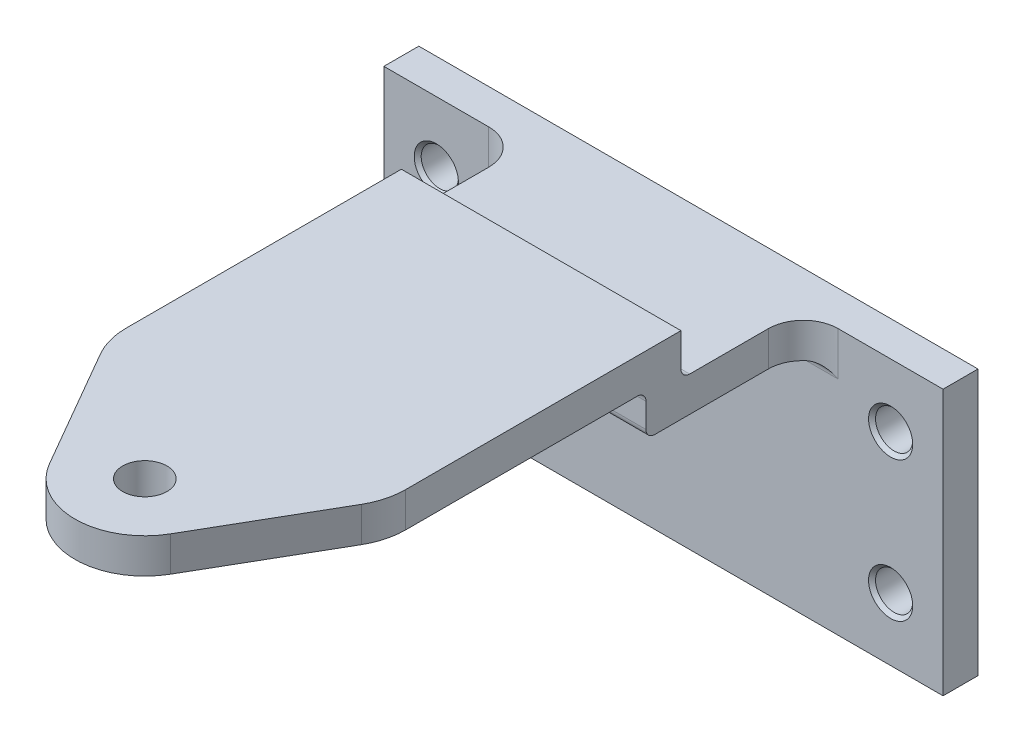
SolidWorks part; units mm, degrees
material "6061-T6 (SS)"
ref_plane "Front Plane" through (0, 0, 0) normal (0, 0, 1) x (1, 0, 0)
ref_plane "Top Plane" through (0, 0, 0) normal (0, 1, 0) x (1, 0, 0)
ref_plane "Right Plane" through (0, 0, 0) normal (1, 0, 0) x (0, 0, -1)
sketch "Sketch1" plane through (0, 0, 0) normal (0, 1, 0) x (1, 0, 0)
  line L0 (0, 0) -> (0, 67.2737) construction
  line L1 (-25.4, 50.8) -> (25.4, 50.8)
  line L2 (25.4, 50.8) -> (25.4, 18.5941)
  line L3 (25.4, 18.5941) -> (10.9985, -6.35)
  line L4 (0, 0) -> (41.2147, 0) construction
  line L5 (-25.4, 18.5941) -> (-10.9985, -6.35)
  line L6 (-25.4, 50.8) -> (-25.4, 18.5941)
  circle A0 centre (0, 0) radius 4.0323
  arc A1 (-10.9985, -6.35) -> (10.9985, -6.35) centre (0, 0) ccw
  point P13 (0, 50.8)
  dimension "D1" = 8.0645
  dimension "D2" = 25.4
  dimension "D3" = 50.8
  dimension "D4" = 50.8
  dimension "D5" = 60
extrude "Boss-Extrude1" add sketch "Sketch1" along normal mid plane 6.35
fillet "Fillet1" radius 12.7 2 edges at (25.4, 0, -18.5941) (-25.4, 0, -18.5941)
sketch "Sketch2" plane through (25.4, 0, 0) normal (1, 0, 0) x (0, 0, -1)
  line L0 (50.8, 3.175) -> (72.009, 3.175)
  line L1 (72.009, 3.175) -> (72.009, -4.445)
  line L2 (72.009, -4.445) -> (100.584, -4.445)
  line L3 (100.584, -4.445) -> (100.584, -52.705)
  line L4 (50.8, 3.175) -> (50.8, -3.175) construction
  line L5 (100.584, -28.575) -> (61.8714, -28.575) construction
  dimension "D1" = 49.784
  dimension "D2" = 28.575
  dimension "D3" = 7.62
  dimension "D4" = 31.75
extrude "Extrude-Thin1" add sketch "Sketch2" against normal up to surface (50.8 mm away) thin
sketch "Sketch3" plane through (25.4, 0, 0) normal (1, 0, 0) x (0, 0, -1)
  line L1 (94.234, -52.705) -> (100.584, -52.705)
  line L2 (94.234, -52.705) -> (94.234, -4.445)
  line L3 (94.234, -4.445) -> (100.584, -4.445)
  line L4 (100.584, -52.705) -> (100.584, -4.445)
extrude "Boss-Extrude2" add sketch "Sketch3" along normal blind 25.4
sketch "Sketch4" plane through (0, 0, -94.234) normal (0, 0, 1) x (1, 0, 0)
  line L0 (50.8, -28.575) -> (41.275, -28.575) construction
  line L1 (50.8, -4.445) -> (50.8, -52.705) construction
  line L2 (41.275, -15.875) -> (41.275, -41.275) construction
  point P6 (41.275, -28.575)
  dimension "D1" = 25.4
  dimension "D2" = 9.525
hole_wizard "1/4 Clearance Hole1" positions "Sketch6" profile "Sketch5" hole size "1/4" standard "Ansi Inch" end condition up to next
sketch "Sketch6" plane through (0, 0, -94.234) normal (0, 0, 1) x (1, 0, 0)
  point P0 (41.275, -15.875)
  point P1 (41.275, -41.275)
sketch "Sketch5" plane through (41.275, -15.875, -94.234) normal (1, 0, 0) x (0, -1, 0)
  line L0 (0, 0) -> (0, 6.35)
  line L1 (0, 6.35) -> (4.0132, 6.35)
  line L2 (3.3782, 5.715) -> (3.3782, 0.635)
  line L3 (3.3782, 0.635) -> (4.0132, 0)
  line L5 (4.0132, 0) -> (0, 0)
  line L6 (-3.3782, 0.635) -> (-4.0132, 0) construction
  line L7 (4.0132, 6.35) -> (3.3782, 5.715)
  line L8 (-4.0132, 6.35) -> (-3.3782, 5.715) construction
  line L11 (0, -6.35) -> (0, 107.95) construction
  dimension "Thru Hole Dia." = 6.7564
  dimension "Thru Hole Depth" = 6.35
  dimension "Near C'Sink Dia." = 8.0264
  dimension "Near C'Sink Angle" = 90
  dimension "Far C'Sink Dia." = 8.0264
  dimension "Far C'Sink Angle" = 90
mirror "Mirror1" about plane through (0, 0, 0) normal (1, 0, 0) of "1/4 Clearance Hole1", "Boss-Extrude2"
fillet "Fillet2" radius 6.35 2 edges at (25.4, -7.62, -94.234) (-25.4, -7.62, -94.234)
fillet "Fillet3" radius 1.5875 4 edges at (0, -4.445, -72.009) (0, -10.795, -65.659) (0, -3.175, -65.659) (0, -10.795, -94.234)
